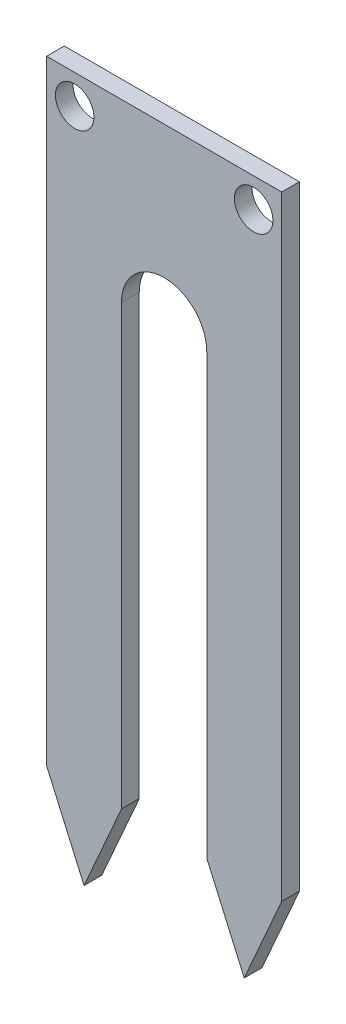
SolidWorks part; units mm, degrees
ref_plane "Plan de face" through (0, 0, 0) normal (0, 0, 1) x (1, 0, 0)
ref_plane "Plan de dessus" through (0, 0, 0) normal (0, 1, 0) x (1, 0, 0)
ref_plane "Plan de droite" through (0, 0, 0) normal (1, 0, 0) x (0, 0, -1)
sketch "Esquisse1" plane through (0, 0, 0) normal (0, 0, 1) x (1, 0, 0)
  line L0 (10.155, 60.41) -> (10.155, 48.93) construction
  line L2 (0, 7.35) -> (0, 60.41)
  line L3 (0, 60.41) -> (20.31, 60.41)
  line L4 (20.31, 7.35) -> (20.31, 60.41)
  line L5 (6.475, 45.25) -> (6.475, 7.35)
  line L6 (13.835, 45.25) -> (13.835, 7.35)
  line L11 (0, 7.35) -> (3.2375, 0)
  line L12 (3.2375, 0) -> (6.475, 7.35)
  line L13 (17.0725, 0) -> (13.835, 7.35)
  line L14 (17.0725, 0) -> (20.31, 7.35)
  arc A0 (13.835, 45.25) -> (6.475, 45.25) centre (10.155, 45.25) ccw
  dimension "D4" = 3.68
  dimension "D1" = 20.31
  dimension "D3" = 11.48
  dimension "D5" = 53.06
  dimension "D6" = 60.41
  dimension "D7" = 6.475
extrude "Boss.-Extru.1" add sketch "Esquisse1" along normal blind 1.53
sketch "Esquisse2" plane through (0, 0, 1.53) normal (0, 0, 1) x (1, 0, 0)
  line L0 (2.425, 60.41) -> (2.425, 57.885) construction
  line L1 (20.31, 60.41) -> (0, 60.41) construction
  line L2 (0, 57.885) -> (2.425, 57.885) construction
  line L3 (0, 60.41) -> (0, 7.35) construction
  line L4 (10.155, 48.93) -> (10.155, 60.41) construction
  circle A0 centre (2.425, 57.885) radius 1.665
  arc A1 (13.835, 45.25) -> (6.475, 45.25) centre (10.155, 45.25) ccw construction
  circle A2 centre (17.885, 57.885) radius 1.665
  dimension "D3" = 3.33
  dimension "D1" = 2.525
  dimension "D2" = 2.425
extrude "Enlèv. mat.-Extru.1" cut sketch "Esquisse2" against normal blind 1.53
